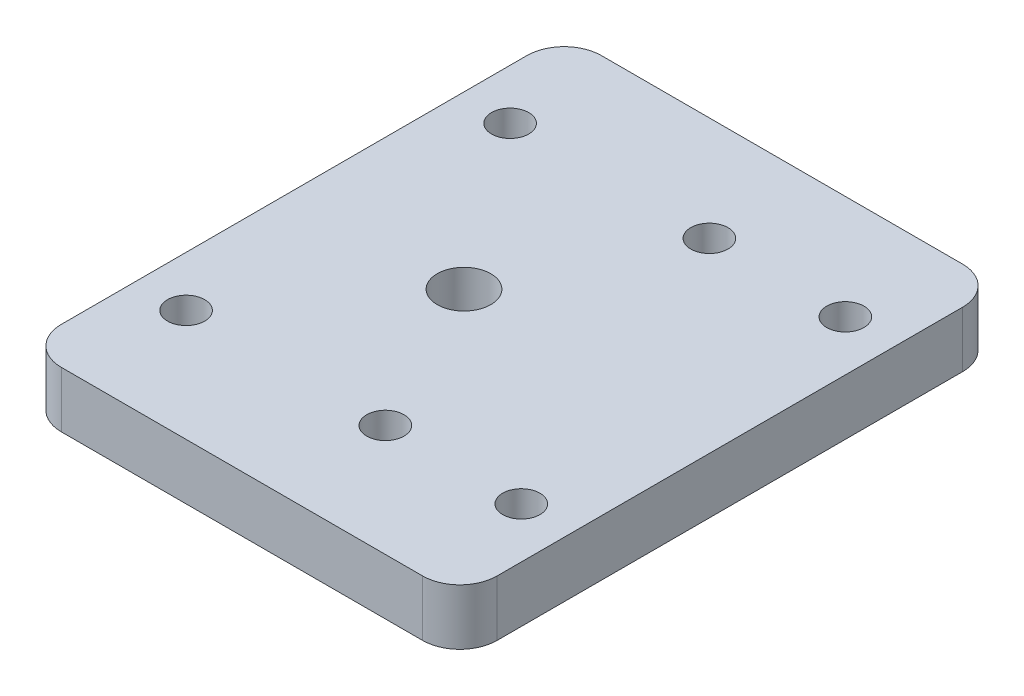
SolidWorks part; units mm, degrees
ref_plane "Front Plane" through (0, 0, 0) normal (0, 0, 1) x (1, 0, 0)
ref_plane "Top Plane" through (0, 0, 0) normal (0, 1, 0) x (1, 0, 0)
ref_plane "Right Plane" through (0, 0, 0) normal (1, 0, 0) x (0, 0, -1)
sketch "Sketch1" plane through (0, 0, 0) normal (0, 1, 0) x (1, 0, 0)
  line L0 (-30.4611, 0) -> (33.997, 0) construction
  line L1 (-11.7, -14.5) -> (11.7, -14.5)
  line L2 (-11.7, -14.5) -> (-11.7, 14.5)
  line L3 (-11.7, 14.5) -> (11.7, 14.5)
  line L4 (11.7, -14.5) -> (11.7, 14.5)
  line L5 (-11.7, -14.5) -> (11.7, 14.5) construction
  line L6 (-11.7, 14.5) -> (11.7, -14.5) construction
  circle A0 centre (9, 8.9) radius 1
  circle A2 centre (9, -8.5) radius 1
  circle A3 centre (-9, -8.5) radius 1
  circle A5 centre (1.7, -8.5) radius 1
  spline S1 degree 3 poles (19.181, -14.2425) (19.8008, -12.3411) (17.8993, -11.7212) (17.2795, -13.6227) (16.6596, -15.5241) (18.5612, -16.144) (19.181, -14.2425) (19.8008, -12.3411) (17.8993, -11.7212) knots -0.5 0 0 0 0.5 0.5 0.5 1 1 1 1.5 1.5 1.5 weights 1 0.333333 0.333333 1 0.333333 0.333333 1 0.333333 0.333333 only from (19.181, -14.2425) to (19.181, -14.2425) construction
  spline S2 degree 3 poles (22.4885, -4.0962) (23.1083, -2.1947) (21.2068, -1.5749) (20.587, -3.4763) (19.9671, -5.3778) (21.8687, -5.9977) (22.4885, -4.0962) (23.1083, -2.1947) (21.2068, -1.5749) knots -0.5 0 0 0 0.5 0.5 0.5 1 1 1 1.5 1.5 1.5 weights 1 0.333333 0.333333 1 0.333333 0.333333 1 0.333333 0.333333 only from (22.4885, -4.0962) to (22.4885, -4.0962) construction
  spline S3 degree 3 poles (19.181, -14.2425) (19.8008, -12.3411) (17.8993, -11.7212) (17.2795, -13.6227) (16.6596, -15.5241) (18.5612, -16.144) (19.181, -14.2425) (19.8008, -12.3411) (17.8993, -11.7212) knots -0.5 0 0 0 0.5 0.5 0.5 1 1 1 1.5 1.5 1.5 weights 1 0.333333 0.333333 1 0.333333 0.333333 1 0.333333 0.333333 only from (19.181, -14.2425) to (19.181, -14.2425)
  spline S4 degree 3 poles (22.4885, -4.0962) (23.1083, -2.1947) (21.2068, -1.5749) (20.587, -3.4763) (19.9671, -5.3778) (21.8687, -5.9977) (22.4885, -4.0962) (23.1083, -2.1947) (21.2068, -1.5749) knots -0.5 0 0 0 0.5 0.5 0.5 1 1 1 1.5 1.5 1.5 weights 1 0.333333 0.333333 1 0.333333 0.333333 1 0.333333 0.333333 only from (22.4885, -4.0962) to (22.4885, -4.0962)
  point P0 (0, 0)
  point P6 (-9, 8.5)
  point P7 (9, 8.5)
  point P8 (9, 8.9)
  point P18 (1.7, 8.5)
  dimension "D7" = 17.4
  dimension "D8" = 18
  dimension "D10" = 2
  dimension "D1" = 29
  dimension "D2" = 23.4
  dimension "D3" = 6
  dimension "D4" = 6
  dimension "D5" = 18
  dimension "D6" = 2.7
  dimension "D9" = 10.7
extrude "Boss-Extrude1" add sketch "Sketch1" along normal blind 3
fillet "Fillet1" radius 2 4 edges at (11.7, 1.5, -14.5) (11.7, 1.5, 14.5) (-11.7, 1.5, 14.5) (-11.7, 1.5, -14.5)
sketch "Sketch5" plane through (0, 0, 0) normal (0, -1, 0) x (1, 0, 0)
  circle A0 centre (-2.1456, 3.6104) radius 2.5 construction
  circle A1 centre (-2.1456, 3.6104) radius 2.5 construction
  circle A2 centre (-2.1456, 3.6104) radius 1.44
  dimension "D1" = 2.88
extrude "Cut-Extrude3" cut sketch "Sketch5" against normal blind 10
sketch "Sketch7" plane through (0, 3, 0) normal (0, 1, 0) x (1, 0, 0)
  spline S0 degree 3 poles (19.181, -14.2425) (19.8008, -12.3411) (17.8993, -11.7212) (17.2795, -13.6227) (16.6596, -15.5241) (18.5612, -16.144) (19.181, -14.2425) (19.8008, -12.3411) (17.8993, -11.7212) knots -0.5 0 0 0 0.5 0.5 0.5 1 1 1 1.5 1.5 1.5 weights 1 0.333333 0.333333 1 0.333333 0.333333 1 0.333333 0.333333 only from (19.181, -14.2425) to (19.181, -14.2425) construction
  spline S1 degree 3 poles (22.4885, -4.0962) (23.1083, -2.1947) (21.2068, -1.5749) (20.587, -3.4763) (19.9671, -5.3778) (21.8687, -5.9977) (22.4885, -4.0962) (23.1083, -2.1947) (21.2068, -1.5749) knots -0.5 0 0 0 0.5 0.5 0.5 1 1 1 1.5 1.5 1.5 weights 1 0.333333 0.333333 1 0.333333 0.333333 1 0.333333 0.333333 only from (22.4885, -4.0962) to (22.4885, -4.0962) construction
  spline S2 degree 3 poles (19.181, -14.2425) (19.8008, -12.3411) (17.8993, -11.7212) (17.2795, -13.6227) (16.6596, -15.5241) (18.5612, -16.144) (19.181, -14.2425) (19.8008, -12.3411) (17.8993, -11.7212) knots -0.5 0 0 0 0.5 0.5 0.5 1 1 1 1.5 1.5 1.5 weights 1 0.333333 0.333333 1 0.333333 0.333333 1 0.333333 0.333333 only from (19.181, -14.2425) to (19.181, -14.2425)
  spline S3 degree 3 poles (22.4885, -4.0962) (23.1083, -2.1947) (21.2068, -1.5749) (20.587, -3.4763) (19.9671, -5.3778) (21.8687, -5.9977) (22.4885, -4.0962) (23.1083, -2.1947) (21.2068, -1.5749) knots -0.5 0 0 0 0.5 0.5 0.5 1 1 1 1.5 1.5 1.5 weights 1 0.333333 0.333333 1 0.333333 0.333333 1 0.333333 0.333333 only from (22.4885, -4.0962) to (22.4885, -4.0962)
extrude "Cut-Extrude4" cut sketch "Sketch7" against normal blind 10
sketch "Sketch8" plane through (0, 3, 0) normal (0, 1, 0) x (1, 0, 0)
  line L0 (24.633, 0) -> (-21.7502, 0) construction
  line L1 (1.7, -8.5) -> (1.7, 20.7764) construction
  line L2 (-9, -8.5) -> (-9, 21.3011) construction
  line L3 (9, -8.5) -> (9, 8.9) construction
  line L4 (14.3582, 8.9) -> (-23.7207, 8.9) construction
  circle A0 centre (1.7, 8.9) radius 1
  circle A1 centre (-9, 8.9) radius 1
  point P15 (1.7, 8.9)
  point P16 (-9, 8.9)
  dimension "D1" = 2
  dimension "D2" = 2
extrude "Cut-Extrude5" cut sketch "Sketch8" against normal blind 10
sketch "Sketch9" plane through (0, 3, 0) normal (0, 1, 0) x (1, 0, 0)
  circle A0 centre (-2.1456, -3.6104) radius 3.027
extrude "Boss-Extrude3" add sketch "Sketch9" against normal up to surface (3 mm away) up to face at (-9, 0, -9.9)
sketch "Sketch10" plane through (0, 3, 0) normal (0, 1, 0) x (1, 0, 0)
  circle A0 centre (-2.524, -0.0532) radius 1.44
  ellipse E0 centre (-2.524, -0.0532) end of major axis (-2.524, -3.3032) minor radius 3.2499 construction
  ellipse E1 centre (-2.524, -0.0532) end of major axis (-2.524, -3.3032) minor radius 3.2499 construction
  dimension "D1" = 2.88
extrude "Cut-Extrude6" cut sketch "Sketch10" against normal blind 3.5
